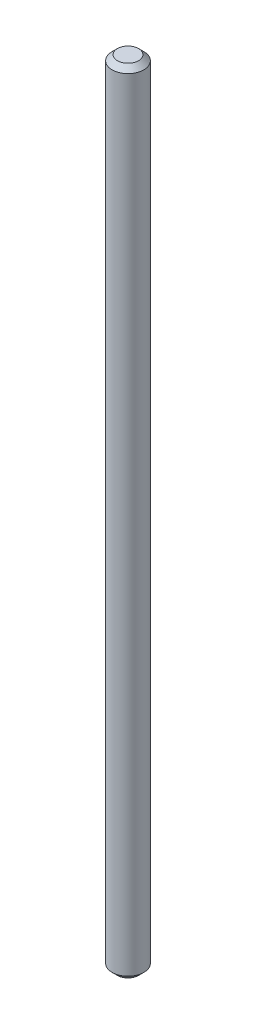
SolidWorks part; units mm, degrees
material "6063-O"
ref_plane "Front Plane" through (0, 0, 0) normal (0, 0, 1) x (1, 0, 0)
ref_plane "Top Plane" through (0, 0, 0) normal (0, 1, 0) x (1, 0, 0)
ref_plane "Right Plane" through (0, 0, 0) normal (1, 0, 0) x (0, 0, -1)
sketch "Sketch1" plane through (0, 0, 0) normal (0, 1, 0) x (1, 0, 0)
  circle A0 centre (0, 0) radius 9
  dimension "D1" = 18
extrude "Boss-Extrude1" add sketch "Sketch1" along normal mid plane 450
chamfer "Chamfer1" distance 3 angle 45 2 edges at (0, 225, 9) (0, -225, 9)
